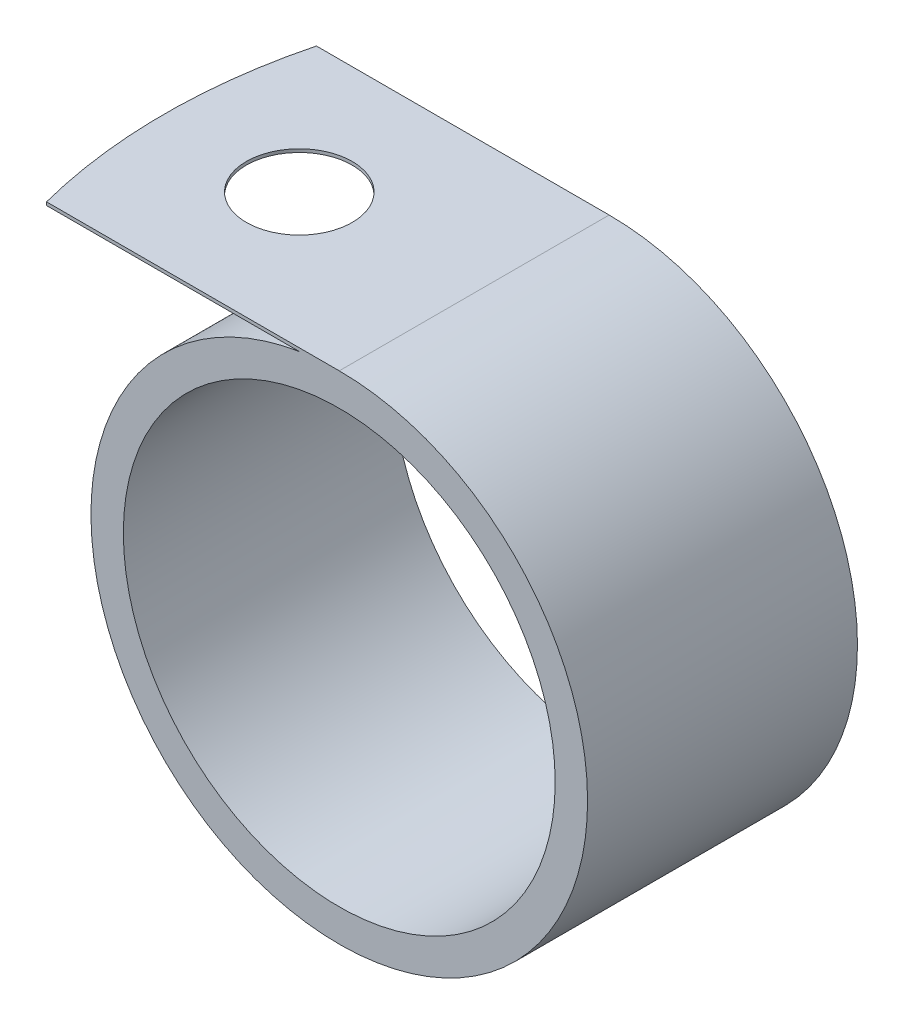
SolidWorks part; units mm, degrees
ref_plane "Front Plane" through (0, 0, 0) normal (0, 0, 1) x (1, 0, 0)
ref_plane "Top Plane" through (0, 0, 0) normal (0, 1, 0) x (1, 0, 0)
ref_plane "Right Plane" through (0, 0, 0) normal (1, 0, 0) x (0, 0, -1)
sketch "Sketch1" plane through (0, 0, 0) normal (0, 0, 1) x (1, 0, 0)
  line L0 (0, 11.684) -> (-14.581, 11.684)
  line L1 (-14.581, 11.684) -> (-14.581, 11.5316)
  line L2 (-14.581, 11.5316) -> (-1.881, 11.5316)
  circle A0 centre (0, 0) radius 10.16
  arc A1 (-1.881, 11.5316) -> (0, 11.684) centre (0, 0) ccw
  dimension "D1" = 20.32
  dimension "D2" = 23.368
  dimension "D3" = 12.7
  dimension "D4" = 0.1524
extrude "Boss-Extrude1" add sketch "Sketch1" along normal mid plane 12.7
sketch "Sketch2" plane through (0, 11.684, 0) normal (0, 1, 0) x (1, 0, 0)
  line L0 (0, 6.35) -> (-14.581, 6.35) construction
  line L1 (0, -6.35) -> (-14.581, -6.35) construction
  line L2 (-14.581, -6.35) -> (-14.581, 6.35) construction
  line L7 (0, 6.35) -> (-14.581, 6.35)
  line L8 (-14.581, 6.35) -> (-14.581, -6.35)
  line L9 (-14.581, -6.35) -> (0, -6.35)
  line L10 (0, -6.35) -> (0, 6.35)
  line L11 (-13.7744, 6.35) -> (-14.581, 6.35)
  line L12 (-14.581, 6.35) -> (-14.581, -6.35)
  line L13 (-14.581, -6.35) -> (-13.7744, -6.35)
  arc A0 (-13.7744, 6.35) -> (-13.7744, -6.35) centre (10.819, 0) ccw
  circle A1 centre (-8.231, 0) radius 2.4892
  line M5 (0, 6.35) -> (-14.581, 6.35)
  line M6 (-14.581, 6.35) -> (-14.581, -6.35)
  line M7 (-14.581, -6.35) -> (0, -6.35)
  dimension "D1" = 25.4
  dimension "D3" = 4.9784
  dimension "D4" = 6.35
  dimension "D2" = 0
extrude "Cut-Extrude1" cut sketch "Sketch2" against normal up to next contours A1 | A0 M5 M6 | A0 L12 M7
